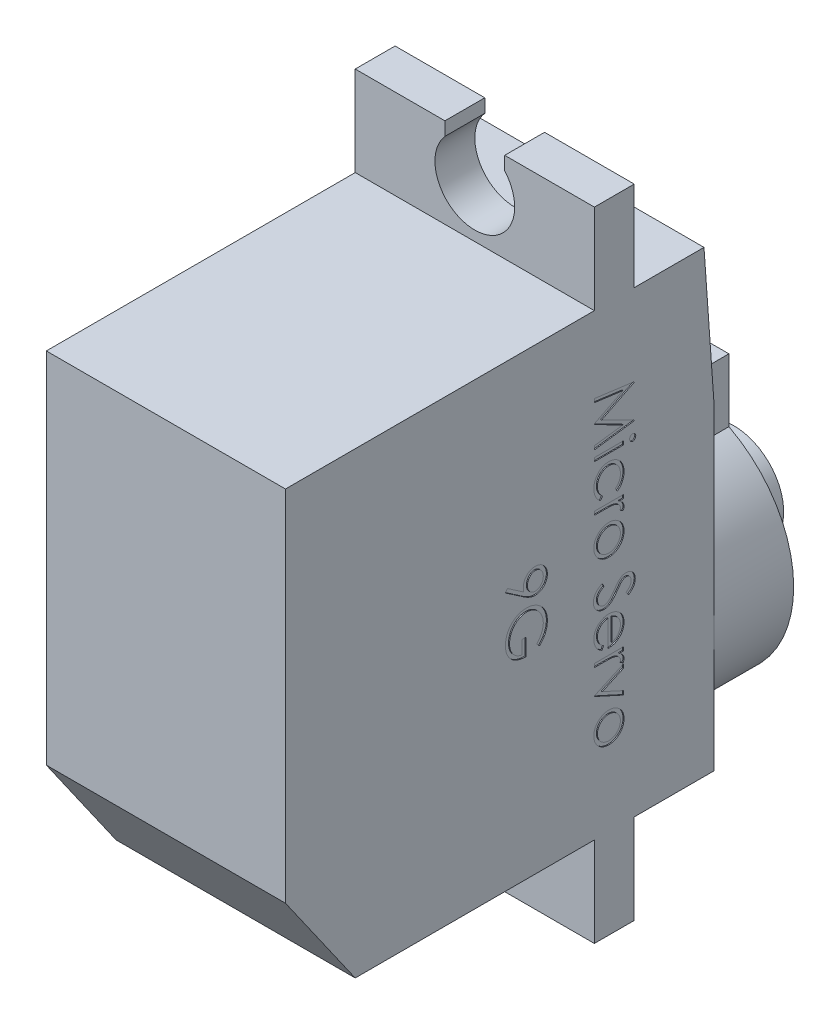
SolidWorks part; units mm, degrees
ref_plane "Ebene vorne" through (0, 0, 0) normal (0, 0, 1) x (1, 0, 0)
ref_plane "Ebene oben" through (0, 0, 0) normal (0, 1, 0) x (1, 0, 0)
ref_plane "Ebene rechts" through (0, 0, 0) normal (1, 0, 0) x (0, 0, -1)
sketch "Skizze1" plane through (0, 0, 0) normal (0, 0, 1) x (1, 0, 0)
  line L0 (0, 30) -> (12, 30) construction
  line L1 (0, 0) -> (4.5, 0)
  line L2 (0, 0) -> (0, 32)
  line L3 (0, 32) -> (4.5, 32)
  line L4 (12, 0) -> (12, 32)
  line L5 (0, 2) -> (12, 2) construction
  line L6 (6, 30) -> (6, 2) construction
  line L7 (4.5, 32) -> (4.5, 0) construction
  line L8 (7.5, 0) -> (7.5, 32) construction
  line L9 (7.5, 31.3229) -> (7.5, 32)
  line L10 (4.5, 31.3229) -> (4.5, 32)
  line L11 (7.5, 0.6771) -> (7.5, 0)
  line L12 (4.5, 0.6771) -> (4.5, 0)
  line L13 (7.5, 32) -> (12, 32)
  line L14 (7.5, 0) -> (12, 0)
  arc A0 (7.5, 0.6771) -> (4.5, 0.6771) centre (6, 2) ccw
  arc A1 (4.5, 31.3229) -> (7.5, 31.3229) centre (6, 30) ccw
  dimension "D5" = 3
  dimension "D1" = 12
  dimension "D2" = 32
  dimension "D3" = 2
  dimension "D4" = 2
  dimension "D6" = 1.5
extrude "Aufsatz-Linear austragen1" add sketch "Skizze1" against normal blind 2
sketch "Skizze2" plane through (0, 0, 0) normal (0, 0, 1) x (1, 0, 0)
  line L0 (0, 32) -> (0, 0) construction
  line L1 (0, 27.5) -> (12, 27.5)
  line L2 (0, 27.5) -> (0, 4.5)
  line L3 (0, 4.5) -> (12, 4.5)
  line L4 (12, 27.5) -> (12, 4.5)
  line L5 (12, 0) -> (12, 32) construction
  line L6 (12, 32) -> (7.5, 32) construction
  line L7 (7.5, 0) -> (12, 0) construction
  dimension "D1" = 4.5
  dimension "D2" = 4.5
extrude "Aufsatz-Linear austragen2" add sketch "Skizze2" along normal blind 15.5 and the other way blind 6
sketch "Skizze3" plane through (12, 0, 0) normal (1, 0, 0) x (0, 0, -1)
  line L0 (5.5, 27.5) -> (6, 20.5)
  line L1 (6, 27.5) -> (2, 27.5) construction
  line L2 (6, 4.5) -> (6, 27.5) construction
  line L3 (5.5, 27.5) -> (6, 27.5)
  line L4 (6, 20.5) -> (6, 27.5)
  line L5 (-15.5, 9.5) -> (-12, 4.5)
  line L6 (-15.5, 4.5) -> (-15.5, 27.5) construction
  line L7 (0, 4.5) -> (-15.5, 4.5) construction
  line L8 (-15.5, 9.5) -> (-15.5, 4.5)
  line L9 (-15.5, 4.5) -> (-12, 4.5)
  dimension "D1" = 5.5
  dimension "D2" = 7
  dimension "D3" = 18
  dimension "D4" = 12
extrude "Schnitt-Linear austragen1" cut sketch "Skizze3" against normal up to next
sketch "Skizze4" plane through (0, 0, -6) normal (0, 0, -1) x (-1, 0, 0)
  line L0 (-6, 4.5) -> (-6, 20.5) construction
  line L1 (0, 4.5) -> (-12, 4.5) construction
  line L2 (0, 20.5) -> (-12, 20.5) construction
  line L3 (-12, 10.5) -> (0, 10.5) construction
  line L4 (-12, 4.5) -> (-12, 20.5) construction
  line L5 (0, 20.5) -> (0, 4.5) construction
  line L6 (-8.75, 15.8327) -> (-8.75, 19)
  line L7 (-8.75, 19) -> (-3.25, 19)
  line L8 (-3.25, 19) -> (-3.25, 15.8327)
  arc A0 (-8.75, 15.8327) -> (-3.25, 15.8327) centre (-6, 10.5) ccw
  dimension "D1" = 6
  dimension "D2" = 5.5
  dimension "D3" = 2.75
  dimension "D4" = 14.5
extrude "Aufsatz-Linear austragen3" add sketch "Skizze4" along normal blind 4
sketch "Skizze5" plane through (0, 0, -10) normal (0, 0, -1) x (-1, 0, 0)
  circle A0 centre (-6, 10.5) radius 2.5
extrude "Aufsatz-Linear austragen4" add sketch "Skizze5" along normal blind 3
sketch "Skizze6" plane through (12, 0, 0) normal (1, 0, 0) x (0, 0, -1)
  line L0 (0, 27.5) -> (0, 4.5) construction
  text T0 "Micro Servo\r\n9G" font "Century Gothic" height 2
extrude "Schnitt-Linear austragen2" cut sketch "Skizze6" against normal blind 0.05
